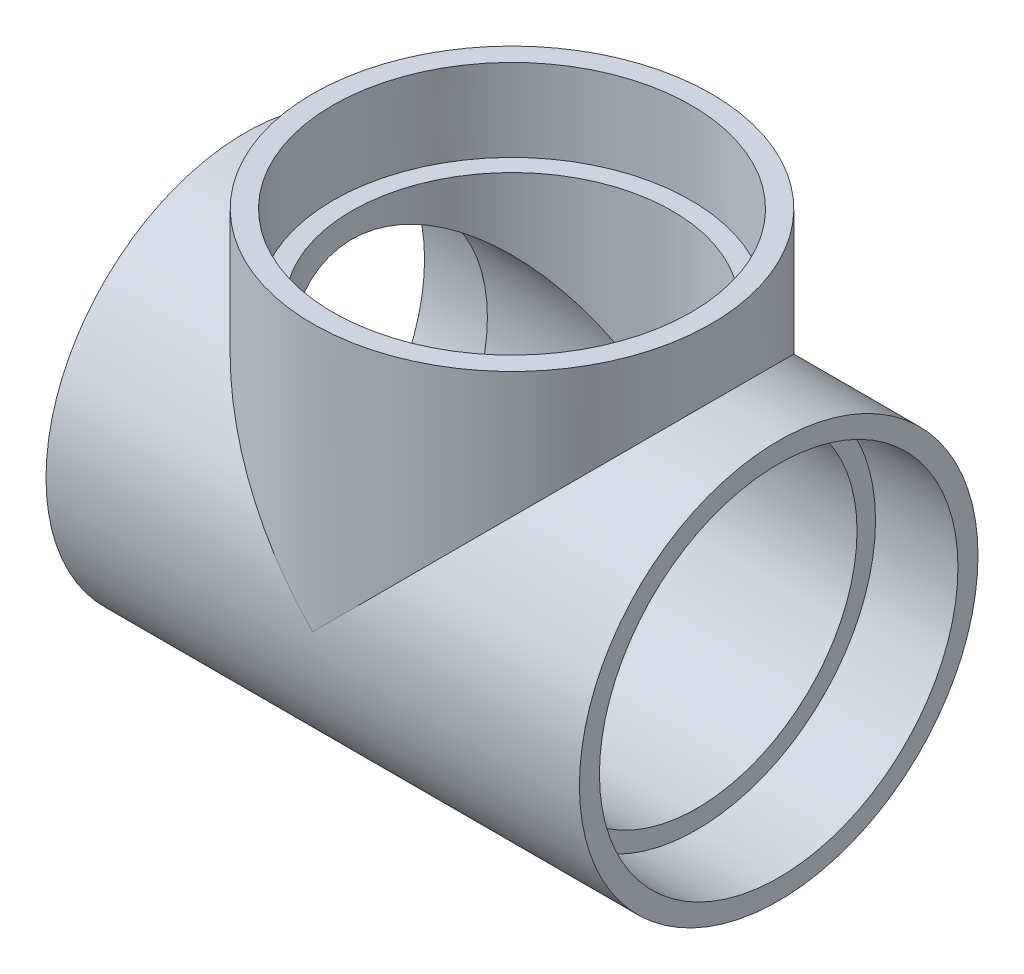
SolidWorks part; units mm, degrees
material "PVC Rigid"
ref_plane "Front Plane" through (0, 0, 0) normal (0, 0, 1) x (1, 0, 0)
ref_plane "Top Plane" through (0, 0, 0) normal (0, 1, 0) x (1, 0, 0)
ref_plane "Right Plane" through (0, 0, 0) normal (1, 0, 0) x (0, 0, -1)
sketch "Sketch0" plane through (0, 0, 0) normal (0, 0, 1) x (1, 0, 0)
  line L0 (-110.5154, 0) -> (0, 0) construction
  line L1 (0, 0) -> (0, 110.5154) construction
  line L2 (-58.9788, 0) -> (0, 0) construction
  line L3 (0, 0) -> (0, 58.9788) construction
  line L4 (-110.5154, 63.6016) -> (-110.5154, -63.6016) construction
  line L5 (-58.9788, 57.0357) -> (-110.5154, 57.3786) construction
  line L6 (-58.9788, 57.0357) -> (-58.9788, -57.0357) construction
  line L7 (-58.9788, -57.0357) -> (-110.5154, -57.3786) construction
  line L8 (-110.5154, 57.3786) -> (-110.5154, -57.3786) construction
  line L9 (-63.6016, 110.5154) -> (63.6016, 110.5154) construction
  line L10 (-57.3786, 110.5154) -> (57.3786, 110.5154) construction
  line L11 (57.3786, 110.5154) -> (57.0357, 58.9788) construction
  line L12 (57.0357, 58.9788) -> (-57.0357, 58.9788) construction
  line L13 (-57.0357, 58.9788) -> (-57.3786, 110.5154) construction
  line L14 (-58.9788, 51.1302) -> (-58.9788, -51.1302) construction
  line L15 (-110.5154, 0) -> (-58.9788, 0) construction
  line L16 (0, 110.5154) -> (0, 58.9788) construction
  line L17 (0, 0) -> (58.9788, 0) construction
  line L18 (-51.1302, 58.9788) -> (51.1302, 58.9788) construction
  line L19 (58.9788, 0) -> (110.5154, 0) construction
  dimension "H" = 110.5154
  dimension "G" = 58.9788
  dimension "M" = 127.2032
  dimension "OD A" = 114.7572
  dimension "OD B" = 114.0714
  dimension "ID" = 102.2604
  dimension "H3" = 110.5154
sketch "Sketch1" plane through (0, 0, 0) normal (0, 0, 1) x (1, 0, 0)
  line L0 (-110.5154, 0) -> (0, 0) construction
  line L1 (-110.5154, 0) -> (0, 0) construction
  line L2 (0, 0) -> (0, -63.6016) construction
  line L3 (-110.5154, -63.6016) -> (-58.9788, -63.6016)
  line L4 (-110.5154, -63.6016) -> (-110.5154, -57.3786)
  line L5 (-110.5154, -57.3786) -> (-58.9788, -57.0357)
  line L6 (-58.9788, -63.6016) -> (-58.9788, -57.0357)
  line L7 (-58.9788, -63.6016) -> (0, -63.6016) construction
  line L8 (110.5154, -57.3786) -> (58.9788, -57.0357)
  line L9 (110.5154, -63.6016) -> (110.5154, -57.3786)
  line L10 (58.9788, -63.6016) -> (58.9788, -57.0357)
  line L11 (110.5154, -63.6016) -> (58.9788, -63.6016)
revolve "Revolve1" add sketch "Sketch1" angle 360 about L1
sketch "Sketch2" plane through (0, 0, 0) normal (0, 0, 1) x (1, 0, 0)
  line L0 (57.3786, 110.5154) -> (57.0357, 58.9788)
  line L1 (57.0357, 58.9788) -> (63.6016, 58.9788)
  line L2 (63.6016, 58.9788) -> (63.6016, 110.5154)
  line L3 (63.6016, 110.5154) -> (57.3786, 110.5154)
  line L4 (0, 0) -> (0, 110.5154) construction
  line L5 (0, 0) -> (0, 110.5154) construction
revolve "Revolve2" add sketch "Sketch2" angle 360 about L5
sketch "Sketch3" plane through (-58.9788, 0, 0) normal (1, 0, 0) x (0, 0, -1)
  circle A0 centre (0, 0) radius 51.1302
  circle A1 centre (0, 0) radius 63.6016
sketch "Sketch4" plane through (-58.9788, 0, 0) normal (1, 0, 0) x (0, 0, -1)
  circle A0 centre (0, 0) radius 63.6016 construction
  circle A1 centre (0, 0) radius 63.6016
extrude "Boss-Extrude1" add sketch "Sketch4" along normal up to vertex
sketch "Sketch5" plane through (0, 58.9788, 0) normal (0, -1, 0) x (1, 0, 0)
  circle A0 centre (0, 0) radius 63.6016 construction
  circle A1 centre (0, 0) radius 63.6016
extrude "Boss-Extrude2" add sketch "Sketch5" along normal up to vertex (58.9788 mm away) up to point (0, 0, 0)
sketch "Sketch6" plane through (0, 0, 0) normal (0, 0, 1) x (1, 0, 0)
  line L0 (-110.5154, -57.3786) -> (-58.9788, -57.0357)
  line L1 (-58.9788, -57.0357) -> (-58.9788, -51.1302)
  line L2 (-58.9788, -51.1302) -> (58.9788, -51.1302)
  line L3 (58.9788, -57.0357) -> (58.9788, 51.8306) construction
  line L4 (0, -51.1302) -> (0, 0) construction
  line L5 (58.9788, -57.0357) -> (58.9788, -51.1302)
  line L6 (110.5154, -57.3786) -> (110.5154, 57.3786) construction
  line L7 (110.5154, -63.6016) -> (110.5154, 63.6016) construction
  line L8 (110.5154, -57.3786) -> (110.5154, 0)
  line L9 (110.5154, 0) -> (-110.5154, 0)
  line L10 (-110.5154, 0) -> (-110.5154, -57.3786)
  line L11 (110.5154, -57.3786) -> (58.9788, -57.0357)
revolve "Cut-Revolve1" cut sketch "Sketch6" angle 360 about L9
sketch "Sketch7" plane through (0, 0, 0) normal (0, 0, 1) x (1, 0, 0)
  line L0 (57.3786, 110.5154) -> (57.0357, 58.9788)
  line L1 (57.0357, 58.9788) -> (51.1302, 58.9788)
  line L2 (51.1302, 58.9788) -> (51.1302, 0)
  line L3 (0, 0) -> (58.9788, 0) construction
  line L4 (51.1302, 0) -> (0, 0)
  line L5 (0, 0) -> (0, 110.5154)
  line L6 (-63.6016, 110.5154) -> (63.6016, 110.5154) construction
  line L7 (0, 110.5154) -> (57.3786, 110.5154)
revolve "Cut-Revolve2" cut sketch "Sketch7" angle 360 about L5
sketch "Sketch8" plane through (0, 110.5154, 0) normal (0, 1, 0) x (1, 0, 0)
  circle A0 centre (0, 0) radius 63.6016 construction
  circle A2 centre (0, 0) radius 63.6016
  circle A3 centre (0, 0) radius 47.3975
extrude "Cut-Extrude1" cut sketch "Sketch8" against normal blind 25.4
sketch "Sketch9" plane through (-110.5154, 0, 0) normal (-1, 0, 0) x (0, 0, 1)
  circle A0 centre (0, 0) radius 79.7265
  circle A1 centre (0, 0) radius 24.8807
extrude "Cut-Extrude2" cut sketch "Sketch9" against normal blind 25.4
sketch "Sketch10" plane through (110.5154, 0, 0) normal (1, 0, 0) x (0, 0, -1)
  circle A0 centre (0, 0) radius 21.9673
  circle A1 centre (0, 0) radius 82.8365
extrude "Cut-Extrude3" cut sketch "Sketch10" against normal blind 25.4
